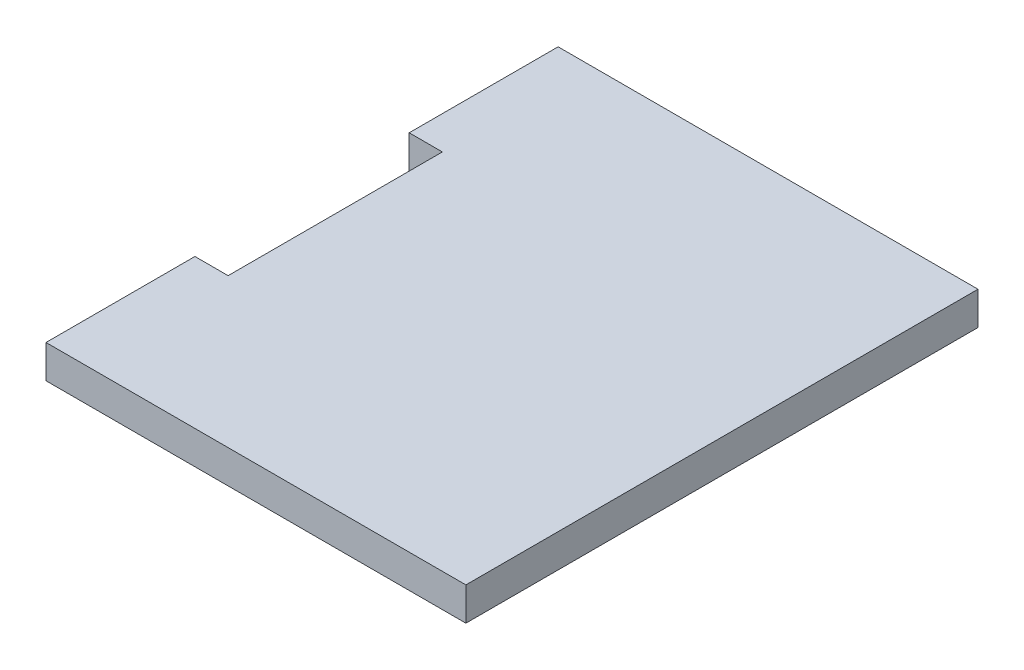
SolidWorks part; units mm, degrees
ref_plane "Front Plane" through (0, 0, 0) normal (0, 0, 1) x (1, 0, 0)
ref_plane "Top Plane" through (0, 0, 0) normal (0, 1, 0) x (1, 0, 0)
ref_plane "Right Plane" through (0, 0, 0) normal (1, 0, 0) x (0, 0, -1)
sketch "Sketch1" plane through (0, 0, 0) normal (0, 1, 0) x (1, 0, 0)
  line L0 (-37, 0) -> (-37, 49) construction
  line L1 (0, 0) -> (-40.175, 0)
  line L2 (0, 0) -> (0, 49)
  line L3 (0, 49) -> (-40.175, 49)
  line L4 (-40.175, 0) -> (-40.175, 49)
  line L6 (-43.35, 14.25) -> (-37, 14.25)
  line L7 (-43.35, 14.25) -> (-43.35, 34.75)
  line L8 (-43.35, 34.75) -> (-37, 34.75)
  line L9 (-37, 14.25) -> (-37, 34.75)
  line L10 (-43.35, 14.25) -> (-37, 34.75) construction
  line L11 (-43.35, 34.75) -> (-37, 14.25) construction
  point P7 (-40.175, 24.5)
  dimension "D1" = 49
  dimension "D3" = 20.5
  dimension "D4" = 37
  dimension "D2" = 3.175
extrude "Boss-Extrude1" add sketch "Sketch1" along normal blind 3.175 contours L9 L6 L4 L1 L2 L3 L8
